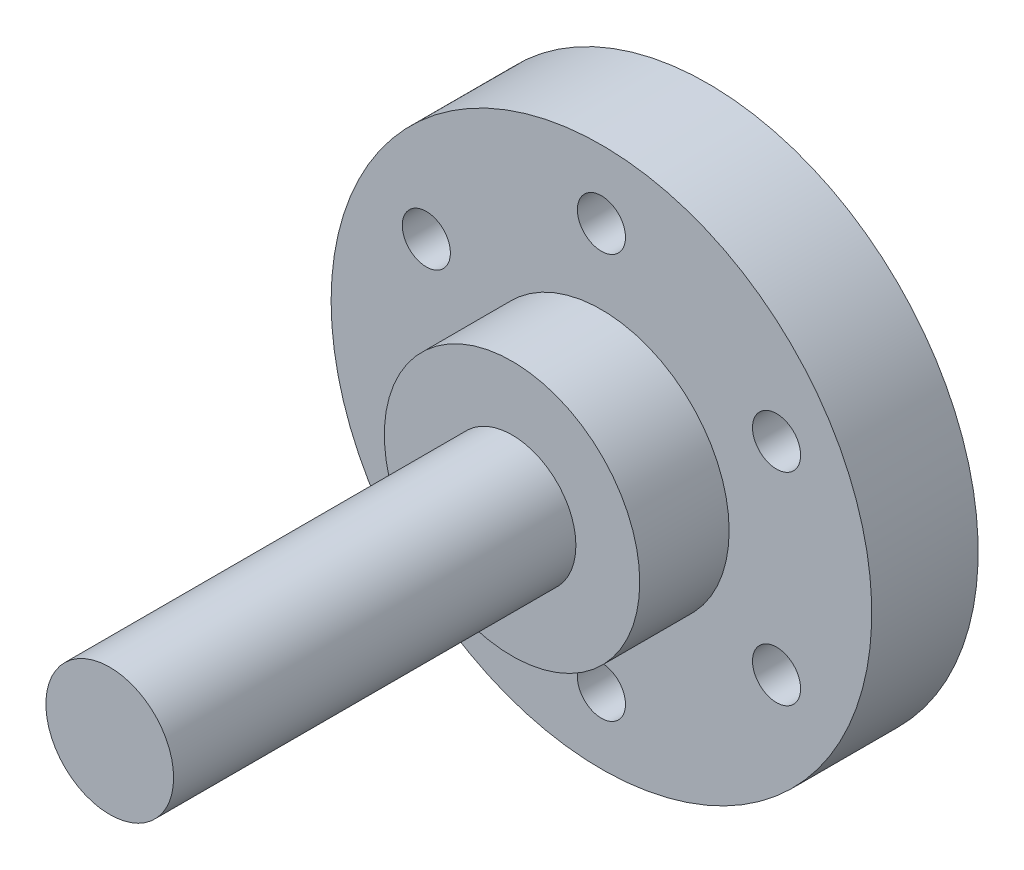
SolidWorks part; units mm, degrees
material "1060 Alloy"
ref_plane "Front Plane" through (0, 0, 0) normal (0, 0, 1) x (1, 0, 0)
ref_plane "Top Plane" through (0, 0, 0) normal (0, 1, 0) x (1, 0, 0)
ref_plane "Right Plane" through (0, 0, 0) normal (1, 0, 0) x (0, 0, -1)
sketch "Sketch1" plane through (0, 0, 0) normal (0, 0, 1) x (1, 0, 0)
  circle A0 centre (0, 0) radius 3
  dimension "D1" = 6
extrude "Boss-Extrude1" add sketch "Sketch1" along normal blind 29
ref_plane "Plane1" through (0, 0, 8) normal (0, 0, 1) x (1, 0, 0)
sketch "Sketch2" plane through (0, 0, 8) normal (0, 0, 1) x (1, 0, 0)
  circle A0 centre (0, 0) radius 6
  dimension "D1" = 12
  dimension "D2" = 12
extrude "Boss-Extrude2" add sketch "Sketch2" against normal blind 2.1
sketch "Sketch3" plane through (0, 0, 5.9) normal (0, 0, -1) x (-1, 0, 0)
  circle A0 centre (0, 0) radius 12.7
  dimension "D1" = 25.4
extrude "Boss-Extrude3" add sketch "Sketch3" along normal blind 5
sketch "Sketch4" plane through (0, 0, 8) normal (0, 0, 1) x (1, 0, 0)
  circle A0 centre (0, 0) radius 6
extrude "Boss-Extrude4" add sketch "Sketch4" along normal blind 2.1
sketch "Sketch10" plane through (0, 0, 0.9) normal (0, 0, -1) x (-1, 0, 0)
  circle A0 centre (8.2272, 4.75) radius 1.4
  circle A1 centre (0, 9.5) radius 1.4
  circle A2 centre (8.2272, -4.75) radius 1.4
  circle A3 centre (0, -9.5) radius 1.4
  circle A4 centre (-8.2272, -4.75) radius 1.4
  circle A5 centre (-8.2272, 4.75) radius 1.4
  point P15 (0, 0)
  dimension "D1" = 6
  dimension "D2" = 2.8
hole_wizard "#4-40 Tapped Hole1" positions "Sketch12" profile "Sketch11" tap size "#4-40" standard "ANSI Inch"
sketch "Sketch12" plane through (0, 0, 0.9) normal (0, 0, -1) x (-1, 0, 0)
  point P0 (8.2272, 4.75)
  point P3 (8.2272, -4.75)
  point P6 (0, -9.5)
  point P9 (-8.2272, -4.75)
  point P12 (-8.2272, 4.75)
  point P15 (0, 9.5)
sketch "Sketch11" plane through (-8.2272, 4.75, 0.9) normal (1, 0, 0) x (0, 1, 0)
  line L0 (0, 0) -> (0, 8.2792)
  line L1 (0, 8.2792) -> (1.1303, 7.6)
  line L2 (1.1303, 7.6) -> (1.1303, 0)
  line L5 (1.1303, 0) -> (0, 0)
  line L10 (0, 8.2792) -> (-1.1303, 7.6) construction
  line L11 (0, -6.35) -> (0, 107.95) construction
  dimension "Tap Drill Dia." = 2.2606
  dimension "Tap Drill Depth" = 7.6
  dimension "Drill Angle" = 118
cosmetic thread "Hole Thread1" parameters "D1"=5, "D2"=2.8448
cosmetic thread "Hole Thread2" parameters "D1"=5, "D2"=2.8448
cosmetic thread "Hole Thread3" parameters "D1"=5, "D2"=2.8448
cosmetic thread "Hole Thread4" parameters "D1"=5, "D2"=2.8448
cosmetic thread "Hole Thread5" parameters "D1"=5, "D2"=2.8448
cosmetic thread "Hole Thread6" parameters "D1"=5, "D2"=2.8448
